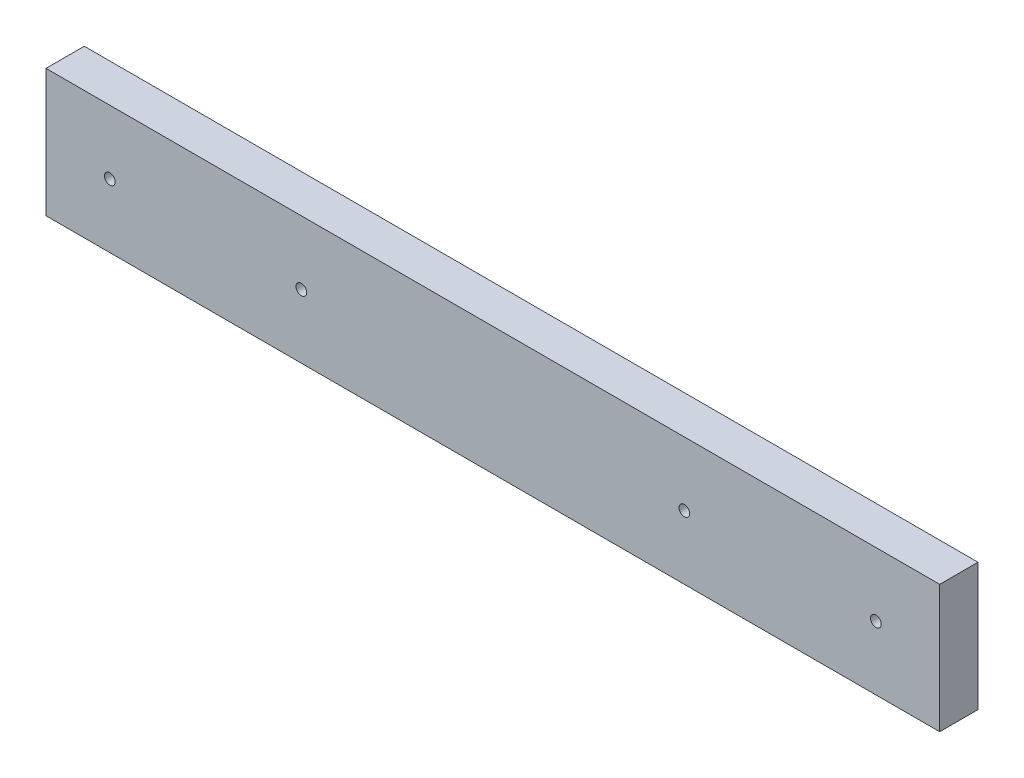
SolidWorks part; units mm, degrees
ref_plane "Ebene vorne" through (0, 0, 0) normal (0, 0, 1) x (1, 0, 0)
ref_plane "Ebene oben" through (0, 0, 0) normal (0, 1, 0) x (1, 0, 0)
ref_plane "Ebene rechts" through (0, 0, 0) normal (1, 0, 0) x (0, 0, -1)
sketch "Skizze1" plane through (0, 0, 0) normal (0, 0, 1) x (1, 0, 0)
  line L1 (-175, -25) -> (175, -25)
  line L2 (-175, -25) -> (-175, 25)
  line L3 (-175, 25) -> (175, 25)
  line L4 (175, -25) -> (175, 25)
  line L5 (-175, -25) -> (175, 25) construction
  line L6 (-175, 25) -> (175, -25) construction
  point P0 (0, 0)
  dimension "D1" = 350
  dimension "D2" = 50
extrude "Aufsatz-Linear austragen1" add sketch "Skizze1" against normal blind 15
hole_wizard "M5 Gewindebohrung1" positions "3D-Skizze2" profile "Skizze3" tap size "M5" standard "DIN"
sketch3d "3D-Skizze2"
  line L0 (-175, 0, 0) -> (175, 0, 0) construction
  line L1 (-175, 25, 0) -> (-175, -25, 0) construction
  line L2 (175, -25, 0) -> (175, 25, 0) construction
  point P7 (-150, 0, 0)
  point P9 (-75, 0, 0)
  point P11 (75, 0, 0)
  point P13 (150, 0, 0)
  point P21 (-130, 0, 0)
  point P22 (0, 0, 0)
  point P23 (0, 0, 0)
  dimension "D1" = 25
  dimension "D2" = 25
  dimension "D3" = 100
  dimension "D4" = 100
sketch "Skizze3" plane through (150, 0, 0) normal (1, 0, 0) x (0, -1, 0)
  line L0 (0, 0) -> (0, 13.2618)
  line L1 (0, 13.2618) -> (2.1, 12)
  line L2 (2.1, 12) -> (2.1, 0)
  line L5 (2.1, 0) -> (0, 0)
  line L10 (0, 13.2618) -> (-2.1, 12) construction
  line L11 (0, -6.35) -> (0, 107.95) construction
  dimension "Bohrerdurchmesser" = 4.2
  dimension "Bohrungstiefe" = 12
  dimension "Spitzenwinkel" = 118
cosmetic thread "Bohrungsgewinde1"
cosmetic thread "Bohrungsgewinde2"
cosmetic thread "Bohrungsgewinde3"
cosmetic thread "Bohrungsgewinde4"
